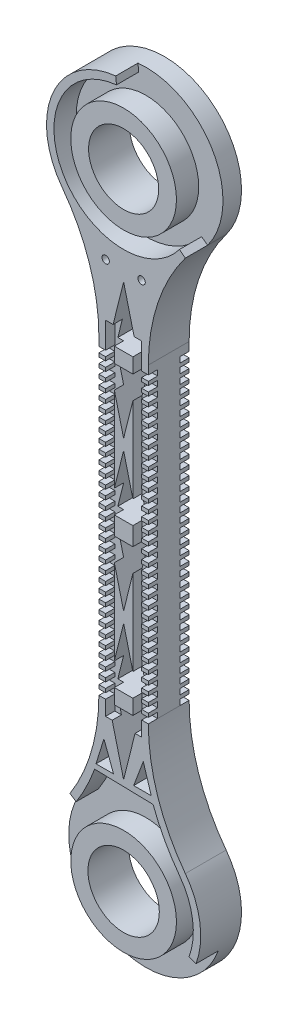
SolidWorks part; units mm, degrees
ref_plane "Front Plane" through (0, 0, 0) normal (0, 0, 1) x (1, 0, 0)
ref_plane "Top Plane" through (0, 0, 0) normal (0, 1, 0) x (1, 0, 0)
ref_plane "Right Plane" through (0, 0, 0) normal (1, 0, 0) x (0, 0, -1)
sketch "leg PIC" plane through (0, 0, 0) normal (0, 0, 1) x (1, 0, 0)
  line L0 (-760.0371, -128.1234) -> (171.2962, -128.1234) construction
sketch "dimension sketch" plane through (0, 0, 0) normal (0, 0, 1) x (1, 0, 0)
  line L0 (0, 0) -> (0, 457.2) construction
  line L1 (0, 0) -> (-301.6354, 0) construction
  line L2 (0, 0) -> (0, -457.2) construction
  dimension "D1" = 457.2
  dimension "D2" = 457.2
sketch "Sketch3" plane through (0, 0, 0) normal (0, 0, 1) x (1, 0, 0)
  line L0 (0, 0) -> (0, 457.2) construction
  line L1 (16.9353, 161.4104) -> (214.8345, 161.4104) construction
  line L2 (-16.9353, 267.8521) -> (-16.9353, 54.9686)
  line L3 (0, 0) -> (0, -457.2) construction
  line L4 (16.9353, 267.8521) -> (16.9353, 54.9686)
  arc A0 (-42.2814, -21.1594) -> (42.2814, -21.1594) centre (0, -52.8237) ccw
  arc A1 (16.9353, 54.9686) -> (42.2814, -21.1594) centre (143.9353, 54.9686) ccw
  arc A2 (-16.9353, 54.9686) -> (-42.2814, -21.1594) centre (-143.9353, 54.9686) cw
  arc A3 (-42.2814, 343.9801) -> (42.2814, 343.9801) centre (0, 375.6444) cw
  arc A4 (-16.9353, 267.8521) -> (-42.2814, 343.9801) centre (-143.9353, 267.8521) ccw
  arc A5 (16.9353, 267.8521) -> (42.2814, 343.9801) centre (143.9353, 267.8521) cw
  point P0 (0, 228.2547)
  dimension "D1" = 127
  dimension "D2" = 212.8835
extrude "main_Bone" add sketch "Sketch3" along normal blind 12.7
sketch "Sketch4" plane through (0, 0, 12.7) normal (0, 0, 1) x (1, 0, 0)
  line L0 (44.8354, -69.2327) -> (49.6059, -70.9786)
  line L1 (-32.4899, -15.9188) -> (-36.7762, -13.1924)
  line L2 (-25.2149, 9.8636) -> (-19.8416, 9.7374)
  line L3 (20.1884, 8.7971) -> (25.676, 8.6681)
  circle A0 centre (0, -52.8237) radius 36.195
  arc A1 (-42.2814, -21.1594) -> (-16.9353, 54.9686) centre (-143.9353, 54.9686) ccw construction
  arc A2 (16.9353, 54.9686) -> (42.2814, -21.1594) centre (143.9353, 54.9686) ccw construction
  arc A3 (-42.2814, -21.1594) -> (42.2814, -21.1594) centre (0, -52.8237) ccw construction
  arc A4 (-36.7762, -13.1924) -> (-25.2149, 9.8636) centre (-143.9353, 54.9686) ccw
  arc A5 (25.676, 8.6681) -> (42.2814, -21.1594) centre (143.9353, 54.9686) ccw
  arc A6 (49.6059, -70.9786) -> (42.2814, -21.1594) centre (0, -52.8237) ccw
  arc A7 (20.1884, 8.7971) -> (38.2153, -24.2045) centre (143.9353, 54.9686) ccw
  arc A8 (44.8354, -69.2327) -> (38.2153, -24.2045) centre (0, -52.8237) ccw
  arc A9 (-32.4899, -15.9188) -> (-19.8416, 9.7374) centre (-143.9353, 54.9686) ccw
  arc A10 (-38.2153, -24.2045) -> (-11.8553, 54.9686) centre (-143.9353, 54.9686) ccw construction
  arc A11 (-42.2814, -21.1594) -> (-16.9353, 54.9686) centre (-143.9353, 54.9686) ccw construction
  arc A12 (-42.2814, -21.1594) -> (42.2814, -21.1594) centre (0, -52.8237) ccw construction
  arc A13 (-38.2153, -24.2045) -> (38.2153, -24.2045) centre (0, -52.8237) ccw construction
  arc A14 (11.8553, 54.9686) -> (38.2153, -24.2045) centre (143.9353, 54.9686) ccw construction
  arc A15 (16.9353, 54.9686) -> (42.2814, -21.1594) centre (143.9353, 54.9686) ccw construction
  dimension "D2" = 72.39
  dimension "D1" = 5.08
extrude "knee _encloser " add sketch "Sketch4" along normal blind 15.24
sketch "Sketch5" plane through (0, 0, 12.7) normal (0, 0, 1) x (1, 0, 0)
  line L0 (-38.2153, 347.0253) -> (-42.2814, 343.9801)
  line L1 (-4.8887, 423.1372) -> (-5.4089, 428.1905)
  circle A0 centre (0, 375.6444) radius 36.195
  arc A1 (42.2814, 343.9801) -> (-42.2814, 343.9801) centre (0, 375.6444) ccw construction
  arc A2 (-5.4089, 428.1905) -> (-42.2814, 343.9801) centre (0, 375.6444) ccw
  arc A3 (-4.8887, 423.1372) -> (-38.2153, 347.0253) centre (0, 375.6444) ccw
  arc A4 (42.2814, 343.9801) -> (-42.2814, 343.9801) centre (0, 375.6444) ccw construction
  arc A5 (38.2153, 347.0253) -> (-38.2153, 347.0253) centre (0, 375.6444) ccw construction
  dimension "D1" = 72.39
  dimension "D2" = 5.08
extrude "thigh_encloser" add sketch "Sketch5" along normal blind 15.24
sketch "Sketch6" plane through (0, 0, 12.7) normal (0, 0, 1) x (1, 0, 0)
  line L2 (-25.2149, 9.8636) -> (25.676, 8.6681)
  line L3 (16.9353, 54.9686) -> (16.9353, 267.8521) construction
  line L4 (-16.9353, 267.8521) -> (-16.9353, 54.9686) construction
  line L5 (16.9353, 54.9686) -> (16.9353, 267.8521)
  line L6 (-16.9353, 267.8521) -> (-16.9353, 54.9686)
  line L7 (-42.2814, 343.9801) -> (-38.2153, 347.0253) construction
  line L8 (-42.2814, 343.9801) -> (-38.2153, 347.0253)
  line L9 (42.2814, 343.9801) -> (38.2153, 347.0253)
  arc A4 (42.2814, 343.9801) -> (16.9353, 267.8521) centre (143.9353, 267.8521) ccw construction
  arc A5 (-16.9353, 267.8521) -> (-42.2814, 343.9801) centre (-143.9353, 267.8521) ccw construction
  arc A6 (-25.2149, 9.8636) -> (-16.9353, 54.9686) centre (-143.9353, 54.9686) ccw construction
  arc A7 (16.9353, 54.9686) -> (25.676, 8.6681) centre (143.9353, 54.9686) ccw construction
  arc A8 (42.2814, 343.9801) -> (16.9353, 267.8521) centre (143.9353, 267.8521) ccw
  arc A9 (-16.9353, 267.8521) -> (-42.2814, 343.9801) centre (-143.9353, 267.8521) ccw
  arc A10 (-25.2149, 9.8636) -> (-16.9353, 54.9686) centre (-143.9353, 54.9686) ccw
  arc A11 (16.9353, 54.9686) -> (25.676, 8.6681) centre (143.9353, 54.9686) ccw
  arc A12 (-38.2153, 347.0253) -> (38.2153, 347.0253) centre (0, 375.6444) ccw
extrude "Boss-Extrude4" add sketch "Sketch6" along normal blind 15.24
sketch "Sketch7" plane through (0, 0, 27.94) normal (0, 0, 1) x (1, 0, 0)
  line L0 (0, 308.7217) -> (0, 13.3584) construction
  line L1 (0, 161.04) -> (39.459, 161.04) construction
  line L2 (16.9353, 54.9686) -> (16.9353, 267.8521) construction
  line L3 (0, 308.7217) -> (-10.2966, 267.4229)
  line L4 (-10.2966, 267.4229) -> (10.2966, 267.4229)
  line L5 (0, 308.7217) -> (10.2966, 267.4229)
  line L6 (0, 262.31) -> (16.9353, 262.31) construction
  line L7 (-10.2966, 257.1971) -> (10.2966, 257.1971)
  line L8 (0, 215.8983) -> (-10.2966, 257.1971)
  line L9 (0, 215.8983) -> (10.2966, 257.1971)
  line L10 (0, 212.2492) -> (16.9353, 212.2492) construction
  line L11 (0, 208.6002) -> (-10.2966, 167.3014)
  line L12 (-10.2966, 167.3014) -> (10.2966, 167.3014)
  line L13 (0, 208.6002) -> (10.2966, 167.3014)
  line L14 (0, 113.4799) -> (10.2966, 154.7787)
  line L15 (-10.2966, 154.7787) -> (10.2966, 154.7787)
  line L16 (0, 113.4799) -> (-10.2966, 154.7787)
  line L17 (0, 106.1818) -> (10.2966, 64.883)
  line L18 (0, 106.1818) -> (-10.2966, 64.883)
  line L19 (-10.2966, 64.883) -> (10.2966, 64.883)
  line L20 (0, 13.3584) -> (10.2966, 54.6572)
  line L21 (-10.2966, 54.6572) -> (10.2966, 54.6572)
  line L22 (0, 13.3584) -> (-10.2966, 54.6572)
  line L29 (-13.4832, 30.9168) -> (-18.9094, 13.3584)
  line L30 (-18.9094, 13.3584) -> (-6.8738, 13.3584)
  line L31 (-6.8738, 13.3584) -> (-13.4832, 30.9168)
  line L32 (18.9094, 13.3584) -> (6.8738, 13.3584)
  line L33 (13.4832, 30.9168) -> (18.9094, 13.3584)
  line L34 (6.8738, 13.3584) -> (13.4832, 30.9168)
  circle A0 centre (0, -52.8237) radius 24.4551
  circle A1 centre (0, 375.6444) radius 24.005
  point P16 (0, 267.4229)
  point P35 (0, 54.6572)
extrude "Cut-Extrude1" cut sketch "Sketch7" against normal through all
sketch "Sketch8" plane through (0, 0, 27.94) normal (0, 0, 1) x (1, 0, 0)
  line L0 (16.9353, 54.9686) -> (12.3633, 54.9686)
  line L1 (12.3633, 54.9686) -> (12.3633, 58.7786)
  line L2 (12.3633, 58.7786) -> (16.9353, 58.7786)
  line L3 (16.9353, 54.9686) -> (16.9353, 267.8521) construction
  line L4 (16.9353, 58.7786) -> (16.9353, 54.9686)
  line L5 (16.9353, 65.1286) -> (16.9353, 61.3186)
  line L6 (12.3633, 65.1286) -> (16.9353, 65.1286)
  line L7 (12.3633, 61.3186) -> (12.3633, 65.1286)
  line L8 (16.9353, 61.3186) -> (12.3633, 61.3186)
  line L9 (16.9353, 71.4786) -> (16.9353, 67.6686)
  line L10 (12.3633, 71.4786) -> (16.9353, 71.4786)
  line L11 (12.3633, 67.6686) -> (12.3633, 71.4786)
  line L12 (16.9353, 67.6686) -> (12.3633, 67.6686)
  line L13 (16.9353, 77.8286) -> (16.9353, 74.0186)
  line L14 (12.3633, 77.8286) -> (16.9353, 77.8286)
  line L15 (12.3633, 74.0186) -> (12.3633, 77.8286)
  line L16 (16.9353, 74.0186) -> (12.3633, 74.0186)
  line L17 (16.9353, 84.1786) -> (16.9353, 80.3686)
  line L18 (12.3633, 84.1786) -> (16.9353, 84.1786)
  line L19 (12.3633, 80.3686) -> (12.3633, 84.1786)
  line L20 (16.9353, 80.3686) -> (12.3633, 80.3686)
  line L21 (16.9353, 90.5286) -> (16.9353, 86.7186)
  line L22 (12.3633, 90.5286) -> (16.9353, 90.5286)
  line L23 (12.3633, 86.7186) -> (12.3633, 90.5286)
  line L24 (16.9353, 86.7186) -> (12.3633, 86.7186)
  line L25 (16.9353, 96.8786) -> (16.9353, 93.0686)
  line L26 (12.3633, 96.8786) -> (16.9353, 96.8786)
  line L27 (12.3633, 93.0686) -> (12.3633, 96.8786)
  line L28 (16.9353, 93.0686) -> (12.3633, 93.0686)
  line L29 (16.9353, 103.2286) -> (16.9353, 99.4186)
  line L30 (12.3633, 103.2286) -> (16.9353, 103.2286)
  line L31 (12.3633, 99.4186) -> (12.3633, 103.2286)
  line L32 (16.9353, 99.4186) -> (12.3633, 99.4186)
  line L33 (16.9353, 109.5786) -> (16.9353, 105.7686)
  line L34 (12.3633, 109.5786) -> (16.9353, 109.5786)
  line L35 (12.3633, 105.7686) -> (12.3633, 109.5786)
  line L36 (16.9353, 105.7686) -> (12.3633, 105.7686)
  line L37 (16.9353, 115.9286) -> (16.9353, 112.1186)
  line L38 (12.3633, 115.9286) -> (16.9353, 115.9286)
  line L39 (12.3633, 112.1186) -> (12.3633, 115.9286)
  line L40 (16.9353, 112.1186) -> (12.3633, 112.1186)
  line L41 (16.9353, 122.2786) -> (16.9353, 118.4686)
  line L42 (12.3633, 122.2786) -> (16.9353, 122.2786)
  line L43 (12.3633, 118.4686) -> (12.3633, 122.2786)
  line L44 (16.9353, 118.4686) -> (12.3633, 118.4686)
  line L45 (16.9353, 128.6286) -> (16.9353, 124.8186)
  line L46 (12.3633, 128.6286) -> (16.9353, 128.6286)
  line L47 (12.3633, 124.8186) -> (12.3633, 128.6286)
  line L48 (16.9353, 124.8186) -> (12.3633, 124.8186)
  line L49 (16.9353, 134.9786) -> (16.9353, 131.1686)
  line L50 (12.3633, 134.9786) -> (16.9353, 134.9786)
  line L51 (12.3633, 131.1686) -> (12.3633, 134.9786)
  line L52 (16.9353, 131.1686) -> (12.3633, 131.1686)
  line L53 (16.9353, 141.3286) -> (16.9353, 137.5186)
  line L54 (12.3633, 141.3286) -> (16.9353, 141.3286)
  line L55 (12.3633, 137.5186) -> (12.3633, 141.3286)
  line L56 (16.9353, 137.5186) -> (12.3633, 137.5186)
  line L57 (16.9353, 147.6786) -> (16.9353, 143.8686)
  line L58 (12.3633, 147.6786) -> (16.9353, 147.6786)
  line L59 (12.3633, 143.8686) -> (12.3633, 147.6786)
  line L60 (16.9353, 143.8686) -> (12.3633, 143.8686)
  line L61 (16.9353, 154.0286) -> (16.9353, 150.2186)
  line L62 (12.3633, 154.0286) -> (16.9353, 154.0286)
  line L63 (12.3633, 150.2186) -> (12.3633, 154.0286)
  line L64 (16.9353, 150.2186) -> (12.3633, 150.2186)
  line L65 (16.9353, 160.3786) -> (16.9353, 156.5686)
  line L66 (12.3633, 160.3786) -> (16.9353, 160.3786)
  line L67 (12.3633, 156.5686) -> (12.3633, 160.3786)
  line L68 (16.9353, 156.5686) -> (12.3633, 156.5686)
  line L69 (16.9353, 166.7286) -> (16.9353, 162.9186)
  line L70 (12.3633, 166.7286) -> (16.9353, 166.7286)
  line L71 (12.3633, 162.9186) -> (12.3633, 166.7286)
  line L72 (16.9353, 162.9186) -> (12.3633, 162.9186)
  line L73 (16.9353, 173.0786) -> (16.9353, 169.2686)
  line L74 (12.3633, 173.0786) -> (16.9353, 173.0786)
  line L75 (12.3633, 169.2686) -> (12.3633, 173.0786)
  line L76 (16.9353, 169.2686) -> (12.3633, 169.2686)
  line L77 (16.9353, 179.4286) -> (16.9353, 175.6186)
  line L78 (12.3633, 179.4286) -> (16.9353, 179.4286)
  line L79 (12.3633, 175.6186) -> (12.3633, 179.4286)
  line L80 (16.9353, 175.6186) -> (12.3633, 175.6186)
  line L81 (16.9353, 185.7786) -> (16.9353, 181.9686)
  line L82 (12.3633, 185.7786) -> (16.9353, 185.7786)
  line L83 (12.3633, 181.9686) -> (12.3633, 185.7786)
  line L84 (16.9353, 181.9686) -> (12.3633, 181.9686)
  line L85 (16.9353, 192.1286) -> (16.9353, 188.3186)
  line L86 (12.3633, 192.1286) -> (16.9353, 192.1286)
  line L87 (12.3633, 188.3186) -> (12.3633, 192.1286)
  line L88 (16.9353, 188.3186) -> (12.3633, 188.3186)
  line L89 (16.9353, 198.4786) -> (16.9353, 194.6686)
  line L90 (12.3633, 198.4786) -> (16.9353, 198.4786)
  line L91 (12.3633, 194.6686) -> (12.3633, 198.4786)
  line L92 (16.9353, 194.6686) -> (12.3633, 194.6686)
  line L93 (16.9353, 204.8286) -> (16.9353, 201.0186)
  line L94 (12.3633, 204.8286) -> (16.9353, 204.8286)
  line L95 (12.3633, 201.0186) -> (12.3633, 204.8286)
  line L96 (16.9353, 201.0186) -> (12.3633, 201.0186)
  line L97 (16.9353, 211.1786) -> (16.9353, 207.3686)
  line L98 (12.3633, 211.1786) -> (16.9353, 211.1786)
  line L99 (12.3633, 207.3686) -> (12.3633, 211.1786)
  line L100 (16.9353, 207.3686) -> (12.3633, 207.3686)
  line L101 (16.9353, 217.5286) -> (16.9353, 213.7186)
  line L102 (12.3633, 217.5286) -> (16.9353, 217.5286)
  line L103 (12.3633, 213.7186) -> (12.3633, 217.5286)
  line L104 (16.9353, 213.7186) -> (12.3633, 213.7186)
  line L105 (16.9353, 223.8786) -> (16.9353, 220.0686)
  line L106 (12.3633, 223.8786) -> (16.9353, 223.8786)
  line L107 (12.3633, 220.0686) -> (12.3633, 223.8786)
  line L108 (16.9353, 220.0686) -> (12.3633, 220.0686)
  line L109 (16.9353, 230.2286) -> (16.9353, 226.4186)
  line L110 (12.3633, 230.2286) -> (16.9353, 230.2286)
  line L111 (12.3633, 226.4186) -> (12.3633, 230.2286)
  line L112 (16.9353, 226.4186) -> (12.3633, 226.4186)
  line L113 (16.9353, 236.5786) -> (16.9353, 232.7686)
  line L114 (12.3633, 236.5786) -> (16.9353, 236.5786)
  line L115 (12.3633, 232.7686) -> (12.3633, 236.5786)
  line L116 (16.9353, 232.7686) -> (12.3633, 232.7686)
  line L117 (16.9353, 242.9286) -> (16.9353, 239.1186)
  line L118 (12.3633, 242.9286) -> (16.9353, 242.9286)
  line L119 (12.3633, 239.1186) -> (12.3633, 242.9286)
  line L120 (16.9353, 239.1186) -> (12.3633, 239.1186)
  line L121 (16.9353, 249.2786) -> (16.9353, 245.4686)
  line L122 (12.3633, 249.2786) -> (16.9353, 249.2786)
  line L123 (12.3633, 245.4686) -> (12.3633, 249.2786)
  line L124 (16.9353, 245.4686) -> (12.3633, 245.4686)
  line L125 (16.9353, 255.6286) -> (16.9353, 251.8186)
  line L126 (12.3633, 255.6286) -> (16.9353, 255.6286)
  line L127 (12.3633, 251.8186) -> (12.3633, 255.6286)
  line L128 (16.9353, 251.8186) -> (12.3633, 251.8186)
  line L129 (16.9353, 261.9786) -> (16.9353, 258.1686)
  line L130 (12.3633, 261.9786) -> (16.9353, 261.9786)
  line L131 (12.3633, 258.1686) -> (12.3633, 261.9786)
  line L132 (16.9353, 258.1686) -> (12.3633, 258.1686)
  line L133 (0, 215.8983) -> (0, 208.6002) construction
  line L134 (-16.9353, 258.1686) -> (-12.3633, 258.1686)
  line L135 (-12.3633, 258.1686) -> (-12.3633, 261.9786)
  line L136 (-12.3633, 261.9786) -> (-16.9353, 261.9786)
  line L137 (-16.9353, 261.9786) -> (-16.9353, 258.1686)
  line L138 (-16.9353, 251.8186) -> (-12.3633, 251.8186)
  line L139 (-12.3633, 251.8186) -> (-12.3633, 255.6286)
  line L140 (-12.3633, 255.6286) -> (-16.9353, 255.6286)
  line L141 (-16.9353, 255.6286) -> (-16.9353, 251.8186)
  line L142 (-16.9353, 245.4686) -> (-12.3633, 245.4686)
  line L143 (-12.3633, 245.4686) -> (-12.3633, 249.2786)
  line L144 (-12.3633, 249.2786) -> (-16.9353, 249.2786)
  line L145 (-16.9353, 249.2786) -> (-16.9353, 245.4686)
  line L146 (-16.9353, 239.1186) -> (-12.3633, 239.1186)
  line L147 (-12.3633, 239.1186) -> (-12.3633, 242.9286)
  line L148 (-12.3633, 242.9286) -> (-16.9353, 242.9286)
  line L149 (-16.9353, 242.9286) -> (-16.9353, 239.1186)
  line L150 (-16.9353, 232.7686) -> (-12.3633, 232.7686)
  line L151 (-12.3633, 232.7686) -> (-12.3633, 236.5786)
  line L152 (-12.3633, 236.5786) -> (-16.9353, 236.5786)
  line L153 (-16.9353, 236.5786) -> (-16.9353, 232.7686)
  line L154 (-16.9353, 226.4186) -> (-12.3633, 226.4186)
  line L155 (-12.3633, 226.4186) -> (-12.3633, 230.2286)
  line L156 (-12.3633, 230.2286) -> (-16.9353, 230.2286)
  line L157 (-16.9353, 230.2286) -> (-16.9353, 226.4186)
  line L158 (-16.9353, 220.0686) -> (-12.3633, 220.0686)
  line L159 (-12.3633, 220.0686) -> (-12.3633, 223.8786)
  line L160 (-12.3633, 223.8786) -> (-16.9353, 223.8786)
  line L161 (-16.9353, 223.8786) -> (-16.9353, 220.0686)
  line L162 (-16.9353, 213.7186) -> (-12.3633, 213.7186)
  line L163 (-12.3633, 213.7186) -> (-12.3633, 217.5286)
  line L164 (-12.3633, 217.5286) -> (-16.9353, 217.5286)
  line L165 (-16.9353, 217.5286) -> (-16.9353, 213.7186)
  line L166 (-16.9353, 207.3686) -> (-12.3633, 207.3686)
  line L167 (-12.3633, 207.3686) -> (-12.3633, 211.1786)
  line L168 (-12.3633, 211.1786) -> (-16.9353, 211.1786)
  line L169 (-16.9353, 211.1786) -> (-16.9353, 207.3686)
  line L170 (-16.9353, 201.0186) -> (-12.3633, 201.0186)
  line L171 (-12.3633, 201.0186) -> (-12.3633, 204.8286)
  line L172 (-12.3633, 204.8286) -> (-16.9353, 204.8286)
  line L173 (-16.9353, 204.8286) -> (-16.9353, 201.0186)
  line L174 (-16.9353, 194.6686) -> (-12.3633, 194.6686)
  line L175 (-12.3633, 194.6686) -> (-12.3633, 198.4786)
  line L176 (-12.3633, 198.4786) -> (-16.9353, 198.4786)
  line L177 (-16.9353, 198.4786) -> (-16.9353, 194.6686)
  line L178 (-16.9353, 188.3186) -> (-12.3633, 188.3186)
  line L179 (-12.3633, 188.3186) -> (-12.3633, 192.1286)
  line L180 (-12.3633, 192.1286) -> (-16.9353, 192.1286)
  line L181 (-16.9353, 192.1286) -> (-16.9353, 188.3186)
  line L182 (-16.9353, 181.9686) -> (-12.3633, 181.9686)
  line L183 (-12.3633, 181.9686) -> (-12.3633, 185.7786)
  line L184 (-12.3633, 185.7786) -> (-16.9353, 185.7786)
  line L185 (-16.9353, 185.7786) -> (-16.9353, 181.9686)
  line L186 (-16.9353, 175.6186) -> (-12.3633, 175.6186)
  line L187 (-12.3633, 175.6186) -> (-12.3633, 179.4286)
  line L188 (-12.3633, 179.4286) -> (-16.9353, 179.4286)
  line L189 (-16.9353, 179.4286) -> (-16.9353, 175.6186)
  line L190 (-16.9353, 169.2686) -> (-12.3633, 169.2686)
  line L191 (-12.3633, 169.2686) -> (-12.3633, 173.0786)
  line L192 (-12.3633, 173.0786) -> (-16.9353, 173.0786)
  line L193 (-16.9353, 173.0786) -> (-16.9353, 169.2686)
  line L194 (-16.9353, 162.9186) -> (-12.3633, 162.9186)
  line L195 (-12.3633, 162.9186) -> (-12.3633, 166.7286)
  line L196 (-12.3633, 166.7286) -> (-16.9353, 166.7286)
  line L197 (-16.9353, 166.7286) -> (-16.9353, 162.9186)
  line L198 (-16.9353, 156.5686) -> (-12.3633, 156.5686)
  line L199 (-12.3633, 156.5686) -> (-12.3633, 160.3786)
  line L200 (-12.3633, 160.3786) -> (-16.9353, 160.3786)
  line L201 (-16.9353, 160.3786) -> (-16.9353, 156.5686)
  line L202 (-16.9353, 150.2186) -> (-12.3633, 150.2186)
  line L203 (-12.3633, 150.2186) -> (-12.3633, 154.0286)
  line L204 (-12.3633, 154.0286) -> (-16.9353, 154.0286)
  line L205 (-16.9353, 154.0286) -> (-16.9353, 150.2186)
  line L206 (-16.9353, 143.8686) -> (-12.3633, 143.8686)
  line L207 (-12.3633, 143.8686) -> (-12.3633, 147.6786)
  line L208 (-12.3633, 147.6786) -> (-16.9353, 147.6786)
  line L209 (-16.9353, 147.6786) -> (-16.9353, 143.8686)
  line L210 (-16.9353, 137.5186) -> (-12.3633, 137.5186)
  line L211 (-12.3633, 137.5186) -> (-12.3633, 141.3286)
  line L212 (-12.3633, 141.3286) -> (-16.9353, 141.3286)
  line L213 (-16.9353, 141.3286) -> (-16.9353, 137.5186)
  line L214 (-16.9353, 131.1686) -> (-12.3633, 131.1686)
  line L215 (-12.3633, 131.1686) -> (-12.3633, 134.9786)
  line L216 (-12.3633, 134.9786) -> (-16.9353, 134.9786)
  line L217 (-16.9353, 134.9786) -> (-16.9353, 131.1686)
  line L218 (-16.9353, 124.8186) -> (-12.3633, 124.8186)
  line L219 (-12.3633, 124.8186) -> (-12.3633, 128.6286)
  line L220 (-12.3633, 128.6286) -> (-16.9353, 128.6286)
  line L221 (-16.9353, 128.6286) -> (-16.9353, 124.8186)
  line L222 (-16.9353, 118.4686) -> (-12.3633, 118.4686)
  line L223 (-12.3633, 118.4686) -> (-12.3633, 122.2786)
  line L224 (-12.3633, 122.2786) -> (-16.9353, 122.2786)
  line L225 (-16.9353, 122.2786) -> (-16.9353, 118.4686)
  line L226 (-16.9353, 112.1186) -> (-12.3633, 112.1186)
  line L227 (-12.3633, 112.1186) -> (-12.3633, 115.9286)
  line L228 (-12.3633, 115.9286) -> (-16.9353, 115.9286)
  line L229 (-16.9353, 115.9286) -> (-16.9353, 112.1186)
  line L230 (-16.9353, 105.7686) -> (-12.3633, 105.7686)
  line L231 (-12.3633, 105.7686) -> (-12.3633, 109.5786)
  line L232 (-12.3633, 109.5786) -> (-16.9353, 109.5786)
  line L233 (-16.9353, 109.5786) -> (-16.9353, 105.7686)
  line L234 (-16.9353, 99.4186) -> (-12.3633, 99.4186)
  line L235 (-12.3633, 99.4186) -> (-12.3633, 103.2286)
  line L236 (-12.3633, 103.2286) -> (-16.9353, 103.2286)
  line L237 (-16.9353, 103.2286) -> (-16.9353, 99.4186)
  line L238 (-16.9353, 93.0686) -> (-12.3633, 93.0686)
  line L239 (-12.3633, 93.0686) -> (-12.3633, 96.8786)
  line L240 (-12.3633, 96.8786) -> (-16.9353, 96.8786)
  line L241 (-16.9353, 96.8786) -> (-16.9353, 93.0686)
  line L242 (-16.9353, 86.7186) -> (-12.3633, 86.7186)
  line L243 (-12.3633, 86.7186) -> (-12.3633, 90.5286)
  line L244 (-12.3633, 90.5286) -> (-16.9353, 90.5286)
  line L245 (-16.9353, 90.5286) -> (-16.9353, 86.7186)
  line L246 (-16.9353, 80.3686) -> (-12.3633, 80.3686)
  line L247 (-12.3633, 80.3686) -> (-12.3633, 84.1786)
  line L248 (-12.3633, 84.1786) -> (-16.9353, 84.1786)
  line L249 (-16.9353, 84.1786) -> (-16.9353, 80.3686)
  line L250 (-16.9353, 74.0186) -> (-12.3633, 74.0186)
  line L251 (-12.3633, 74.0186) -> (-12.3633, 77.8286)
  line L252 (-12.3633, 77.8286) -> (-16.9353, 77.8286)
  line L253 (-16.9353, 77.8286) -> (-16.9353, 74.0186)
  line L254 (-16.9353, 67.6686) -> (-12.3633, 67.6686)
  line L255 (-12.3633, 67.6686) -> (-12.3633, 71.4786)
  line L256 (-12.3633, 71.4786) -> (-16.9353, 71.4786)
  line L257 (-16.9353, 71.4786) -> (-16.9353, 67.6686)
  line L258 (-16.9353, 61.3186) -> (-12.3633, 61.3186)
  line L259 (-12.3633, 61.3186) -> (-12.3633, 65.1286)
  line L260 (-12.3633, 65.1286) -> (-16.9353, 65.1286)
  line L261 (-16.9353, 65.1286) -> (-16.9353, 61.3186)
  line L262 (-16.9353, 58.7786) -> (-16.9353, 54.9686)
  line L263 (-12.3633, 58.7786) -> (-16.9353, 58.7786)
  line L264 (-12.3633, 54.9686) -> (-12.3633, 58.7786)
  line L265 (-16.9353, 54.9686) -> (-12.3633, 54.9686)
  dimension "D1" = 4.572
  dimension "D2" = 3.81
  dimension "D3" = 33
extrude "Cut-Extrude2" cut sketch "Sketch8" against normal blind 6.35
sketch "Sketch9" plane through (0, 0, 27.94) normal (0, 0, 1) x (1, 0, 0)
  line L0 (12.3633, 44.7764) -> (6.3484, 44.7764)
  line L1 (12.3633, 44.7764) -> (12.3633, 279.8224)
  line L2 (6.3484, 44.7764) -> (6.3484, 279.8224)
  line L3 (12.3633, 279.8224) -> (6.3484, 279.8224)
  line L4 (0, 215.8983) -> (0, 208.6002) construction
  line L5 (-12.3633, 279.8224) -> (-6.3484, 279.8224)
  line L6 (-6.3484, 44.7764) -> (-6.3484, 279.8224)
  line L7 (-12.3633, 44.7764) -> (-12.3633, 279.8224)
  line L8 (-12.3633, 44.7764) -> (-6.3484, 44.7764)
extrude "Cut-Extrude3" cut sketch "Sketch9" against normal up to surface (6.35 mm away) up to face at (14.6493, 234.6736, 21.59)
sketch "Sketch10" plane through (-16.9353, 0, 0) normal (-1, 0, 0) x (0, 0, 1)
  line L0 (13.97, 267.8521) -> (13.97, 54.9686) construction
  line L1 (27.94, 267.8521) -> (0, 267.8521) construction
  line L2 (21.59, 54.9686) -> (0, 54.9686) construction
  line L3 (13.97, 54.9686) -> (13.97, 267.8521) construction
sketch "Sketch11" plane through (16.9353, 0, 0) normal (1, 0, 0) x (0, 0, -1)
  line L0 (-13.97, 267.8521) -> (-13.97, 54.9686) construction
ref_plane "Plane1" through (0, 0, 13.97) normal (0, 0, 1) x (1, 0, 0)
mirror "Mirror2" about plane through (0, 0, 13.97) normal (0, 0, 1) of "Cut-Extrude2", "Cut-Extrude3"
sketch "Sketch12" plane through (0, 0, 27.94) normal (0, 0, 1) x (1, 0, 0)
  line L0 (0, 308.7217) -> (0, 323.346) construction
  circle A0 centre (-12.2958, 315.8346) radius 2.54
  circle A1 centre (12.2958, 315.8346) radius 2.54
extrude "Cut-Extrude4" cut sketch "Sketch12" against normal through all
